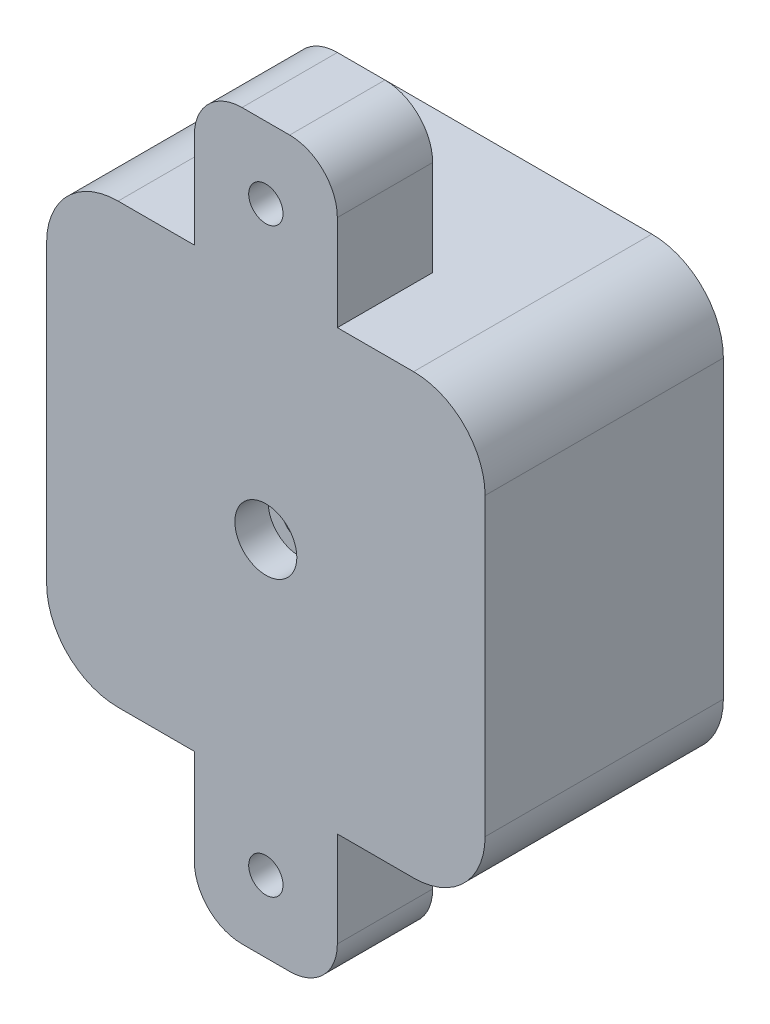
SolidWorks part; units mm, degrees
ref_plane "Plano frontal" through (0, 0, 0) normal (0, 0, 1) x (1, 0, 0)
ref_plane "Plano superior" through (0, 0, 0) normal (0, 1, 0) x (1, 0, 0)
ref_plane "Plano direito" through (0, 0, 0) normal (1, 0, 0) x (0, 0, -1)
other "Saida da Correia"
other "Test"
sketch "Sketch1" plane through (0, 0, 0) normal (0, 0, 1) x (1, 0, 0)
  line L1 (-15.5, 23) -> (15.5, 23)
  line L2 (-23, 15.5) -> (-23, -15.5)
  line L3 (-15.5, -23) -> (15.5, -23)
  line L4 (23, 15.5) -> (23, -15.5)
  line L5 (-23, 23) -> (23, -23) construction
  line L6 (-23, -23) -> (23, 23) construction
  arc A0 (15.5, -23) -> (23, -15.5) centre (15.5, -15.5) ccw
  arc A1 (15.5, 23) -> (23, 15.5) centre (15.5, 15.5) cw
  arc A2 (-15.5, 23) -> (-23, 15.5) centre (-15.5, 15.5) ccw
  arc A3 (-23, -15.5) -> (-15.5, -23) centre (-15.5, -15.5) ccw
  point P0 (0, 0)
  dimension "D3" = 7.5
  dimension "D1" = 46
  dimension "D2" = 46
extrude "Main" add sketch "Sketch1" along normal blind 25
sketch "Sketch2" plane through (0, 0, 0) normal (0, 0, -1) x (-1, 0, 0)
  circle A0 centre (0, 0) radius 20
  dimension "D1" = 40
extrude "Pulley Hole" cut sketch "Sketch2" against normal blind 21
sketch "Sketch3" plane through (-23, 0, 0) normal (-1, 0, 0) x (0, 0, 1)
  line L0 (25, 15.5) -> (25, -15.5) construction
  line L1 (18, -15) -> (8, -15)
  line L2 (18, -15) -> (18, 15)
  line L3 (18, 15) -> (8, 15)
  line L4 (8, -15) -> (8, 15)
  line L6 (25, 15.5) -> (0, 15.5) construction
  dimension "D1" = 7
  dimension "D2" = 10
  dimension "D3" = 30
  dimension "D4" = 0.5
extrude "Pulley Out" cut sketch "Sketch3" against normal up to next
sketch "Sketch4" plane through (0, 0, 25) normal (0, 0, 1) x (1, 0, 0)
  line L0 (23, 0) -> (-23, 0) construction
  line L1 (23, -15.5) -> (23, 15.5) construction
  line L2 (-23, 15.5) -> (-23, -15.5) construction
  line L3 (-15.5, -23) -> (15.5, -23) construction
  line L4 (-7.5, -23) -> (7.5, -23)
  line L5 (-7.5, -23) -> (-7.5, -33)
  line L6 (-2.5, -38) -> (2.5, -38)
  line L7 (7.5, -23) -> (7.5, -33)
  line L8 (-7.5, 23) -> (7.5, 23)
  line L9 (7.5, 23) -> (7.5, 33)
  line L10 (-2.5, 38) -> (2.5, 38)
  line L11 (-7.5, 23) -> (-7.5, 33)
  arc A0 (-2.5, 38) -> (-7.5, 33) centre (-2.5, 33) ccw
  arc A1 (7.5, 33) -> (2.5, 38) centre (2.5, 33) ccw
  arc A2 (2.5, -38) -> (7.5, -33) centre (2.5, -33) ccw
  arc A3 (-7.5, -33) -> (-2.5, -38) centre (-2.5, -33) ccw
  point P19 (-7.5, 38)
  point P22 (7.5, 38)
  point P25 (7.5, -38)
  point P28 (-7.5, -38)
  dimension "D4" = 5
  dimension "D1" = 15
  dimension "D2" = 15
  dimension "D3" = 8
extrude "Fixation" add sketch "Sketch4" against normal blind 10
sketch "Sketch5" plane through (0, 0, 21) normal (0, 0, -1) x (-1, 0, 0)
  circle A0 centre (0, 0) radius 3.5
  dimension "D1" = 7
extrude "Boss-Extrude3" add sketch "Sketch5" along normal blind 4
hole_wizard "M3 Clearance Hole2" positions "3DSketch6" profile "Sketch12" hole size "M3" standard "ANSI Metric" end condition up to next
sketch3d "3DSketch6"
  line L0 (-20.8033, 20.8033, 25) -> (20.8033, -20.8033, 25) construction
  line L2 (20.8033, 20.8033, 25) -> (-20.8033, -20.8033, 25) construction
  arc A0 (-15.5, 23, 25) -> (-23, 15.5, 25) centre (-15.5, 15.5, 25) ccw construction
  arc A1 (15.5, -23, 25) -> (23, -15.5, 25) centre (15.5, -15.5, 25) ccw construction
  arc A2 (23, 15.5, 25) -> (15.5, 23, 25) centre (15.5, 15.5, 25) ccw construction
  arc A3 (-23, -15.5, 25) -> (-15.5, -23, 25) centre (-15.5, -15.5, 25) ccw construction
  point P0 (0, 0, 25)
  point P8 (-15.5, 15.5, 32.5)
  point P12 (15.5, -15.5, 32.5)
  point P19 (15.5, 15.5, 32.5)
  point P23 (-15.5, -15.5, 32.5)
sketch "Sketch12" plane through (0, 0, 25) normal (1, 0, 0) x (0, -1, 0)
  line L0 (0, 0) -> (0, 8)
  line L1 (0, 8) -> (1.8, 8)
  line L2 (1.8, 8) -> (1.8, 0)
  line L5 (1.8, 0) -> (0, 0)
  line L11 (0, -6.35) -> (0, 107.95) construction
  dimension "Thru Hole Dia." = 3.6
  dimension "Thru Hole Depth" = 8
hole_wizard "M3 Clearance Hole3" positions "3DSketch7" profile "Sketch13" hole size "M3" standard "ANSI Metric" end condition up to next
sketch3d "3DSketch7"
  line L0 (-7.5, -23, 25) -> (6.0355, -36.5355, 25) construction
  line L2 (7.5, -23, 25) -> (-6.0355, -36.5355, 25) construction
  arc A0 (2.5, -38, 25) -> (7.5, -33, 25) centre (2.5, -33, 25) ccw construction
  arc A1 (-7.5, -33, 25) -> (-2.5, -38, 25) centre (-2.5, -33, 25) ccw construction
  point P0 (0, -30.5, 25)
  point P9 (2.5, -33, 30)
  point P17 (-2.5, -33, 30)
sketch "Sketch13" plane through (0, -30.5, 25) normal (1, 0, 0) x (0, -1, 0)
  line L0 (0, 0) -> (0, 10)
  line L1 (0, 10) -> (1.8, 10)
  line L2 (1.8, 10) -> (1.8, 0)
  line L5 (1.8, 0) -> (0, 0)
  line L11 (0, -6.35) -> (0, 107.95) construction
  dimension "Thru Hole Dia." = 3.6
  dimension "Thru Hole Depth" = 10
hole_wizard "M3 Clearance Hole4" positions "3DSketch8" profile "Sketch14" hole size "M3" standard "ANSI Metric" end condition up to next
sketch3d "3DSketch8"
  line L0 (-6.0355, 36.5355, 25) -> (7.5, 23, 25) construction
  line L2 (6.0355, 36.5355, 25) -> (-7.5, 23, 25) construction
  arc A0 (-2.5, 38, 25) -> (-7.5, 33, 25) centre (-2.5, 33, 25) ccw construction
  arc A1 (7.5, 33, 25) -> (2.5, 38, 25) centre (2.5, 33, 25) ccw construction
  point P0 (0, 30.5, 25)
  point P6 (-2.5, 33, 30)
  point P14 (2.5, 33, 30)
sketch "Sketch14" plane through (0, 30.5, 25) normal (1, 0, 0) x (0, -1, 0)
  line L0 (0, 0) -> (0, 10)
  line L1 (0, 10) -> (1.8, 10)
  line L2 (1.8, 10) -> (1.8, 0)
  line L5 (1.8, 0) -> (0, 0)
  line L11 (0, -6.35) -> (0, 107.95) construction
  dimension "Thru Hole Dia." = 3.6
  dimension "Thru Hole Depth" = 10
sketch "Sketch15" plane through (0, 0, 25) normal (0, 0, 1) x (1, 0, 0)
  circle A0 centre (0, 0) radius 3.25
  dimension "D1" = 6.5
extrude "Cut-Extrude1" cut sketch "Sketch15" against normal blind 3.5
